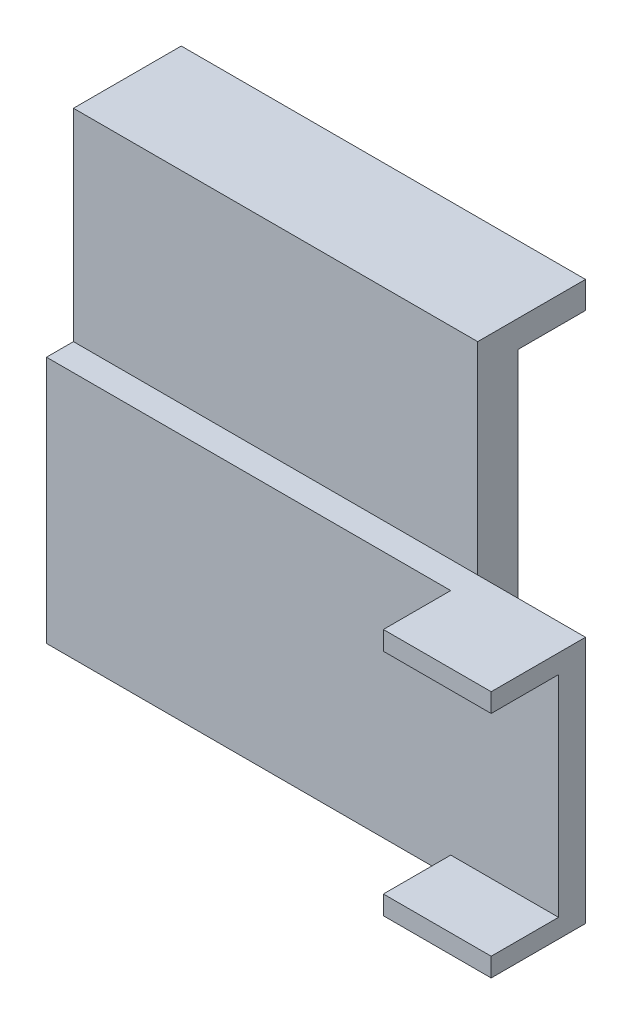
SolidWorks part; units mm, degrees
material "PPE"
ref_plane "Front Plane" through (0, 0, 0) normal (0, 0, 1) x (1, 0, 0)
ref_plane "Top Plane" through (0, 0, 0) normal (0, 1, 0) x (1, 0, 0)
ref_plane "Right Plane" through (0, 0, 0) normal (1, 0, 0) x (0, 0, -1)
sketch "Sketch2" plane through (0, 0, 0) normal (0, 0, 1) x (1, 0, 0)
  line L1 (-25.4, -11.684) -> (25.4, -11.684)
  line L2 (-25.4, -11.684) -> (-25.4, 11.684)
  line L3 (-25.4, 11.684) -> (25.4, 11.684)
  line L4 (25.4, -11.684) -> (25.4, 11.684)
  line L5 (-25.4, -11.684) -> (25.4, 11.684) construction
  line L6 (-25.4, 11.684) -> (25.4, -11.684) construction
  point P0 (0, 0)
  dimension "D1" = 50.8
  dimension "D2" = 23.368
extrude "Boss-Extrude1" add sketch "Sketch2" along normal blind 2.54
sketch "Sketch3" plane through (0, 0, 2.54) normal (0, 0, 1) x (1, 0, 0)
  line L0 (25.4, -11.684) -> (25.4, 11.684) construction
  line L3 (12.7, 9.906) -> (12.7, -9.906) construction
  line L4 (25.4, 11.684) -> (12.7, 11.684)
  line L5 (25.4, 11.684) -> (25.4, 9.906)
  line L6 (25.4, 9.906) -> (12.7, 9.906)
  line L7 (12.7, 11.684) -> (12.7, 9.906)
  line L8 (25.4, -11.684) -> (12.7, -11.684)
  line L9 (25.4, -11.684) -> (25.4, -9.906)
  line L10 (25.4, -9.906) -> (12.7, -9.906)
  line L11 (12.7, -11.684) -> (12.7, -9.906)
  dimension "D1" = 19.812
  dimension "D2" = 12.7
extrude "Boss-Extrude2" add sketch "Sketch3" along normal blind 6.35
sketch "Sketch4" plane through (0, 11.684, 0) normal (0, 1, 0) x (1, 0, 0)
  line L1 (25.4, -8.89) -> (22.86, -8.89)
  line L2 (25.4, -8.89) -> (25.4, 0)
  line L3 (25.4, 0) -> (22.86, 0)
  line L4 (22.86, -8.89) -> (22.86, 0)
  dimension "D1" = 8.89
  dimension "D2" = 2.54
extrude "Cut-Extrude1" cut sketch "Sketch4" against normal through all
sketch "Sketch5" plane through (0, 0, 0) normal (0, 0, -1) x (-1, 0, 0)
  line L5 (25.4, -11.684) -> (-22.86, -11.684) construction
  line L7 (25.4, 11.684) -> (25.4, -11.684)
  line L8 (25.4, -11.684) -> (-12.7, -11.684)
  line L9 (-12.7, 11.684) -> (-12.7, -11.684)
  line L11 (-12.7, 11.684) -> (-12.7, 30.734)
  line L12 (-12.7, 30.734) -> (25.4, 30.734)
  line L13 (25.4, 11.684) -> (25.4, 30.734)
  dimension "D1" = 38.1
  dimension "D2" = 42.418
extrude "Boss-Extrude3" add sketch "Sketch5" along normal blind 3.81
sketch "Sketch10" plane through (0, 0, -3.81) normal (0, 0, -1) x (-1, 0, 0)
  line L0 (25.4, -11.684) -> (25.4, 30.734) construction
  line L1 (-12.7, 30.734) -> (25.4, 30.734)
  line L2 (-12.7, 30.734) -> (-12.7, 28.194)
  line L3 (-12.7, 28.194) -> (25.4, 28.194)
  line L4 (25.4, 30.734) -> (25.4, 28.194)
  dimension "D1" = 2.54
extrude "Boss-Extrude6" add sketch "Sketch10" along normal blind 6.35
scale "Scale1" scale about centroid uniform scaling yes scale factor 1.02
ref_plane "Plane1" through (0, 0, -12.7) normal (0, 0, 1) x (1, 0, 0)
